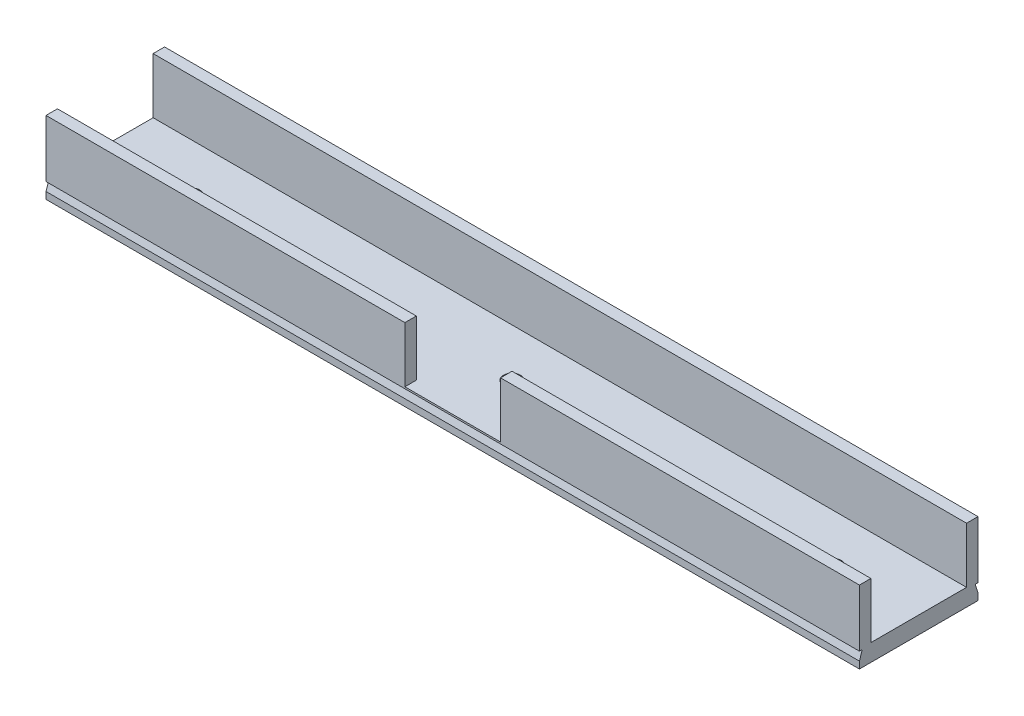
SolidWorks part; units mm, degrees
ref_plane "Front Plane" through (0, 0, 0) normal (0, 0, 1) x (1, 0, 0)
ref_plane "Top Plane" through (0, 0, 0) normal (0, 1, 0) x (1, 0, 0)
ref_plane "Right Plane" through (0, 0, 0) normal (1, 0, 0) x (0, 0, -1)
sketch "Croquis1" plane through (0, 0, 0) normal (0, 1, 0) x (1, 0, 0)
  line L0 (-71, -12.5) -> (-71, 12.5)
  line L1 (-71, -12.5) -> (71, -12.5)
  line L2 (-71, 12.5) -> (71, 12.5)
  line L3 (71, -12.5) -> (71, 12.5)
  line L4 (-71, -12.5) -> (71, 12.5) construction
  line L5 (-71, 12.5) -> (71, -12.5) construction
  line L6 (71, -10.35) -> (71, 10.35)
  line L7 (71, -10.35) -> (-71, -10.35)
  line L8 (71, 10.35) -> (-71, 10.35)
  line L9 (-71, -10.35) -> (-71, 10.35)
  line L10 (71, -10.35) -> (-71, 10.35) construction
  line L11 (71, 10.35) -> (-71, -10.35) construction
  point P1 (0, 0)
  point P2 (0, 0)
  dimension "D1" = 142
  dimension "D2" = 25
  dimension "D3" = 142
  dimension "D4" = 2.15
extrude "Saliente-Extruir2" add sketch "Croquis1" along normal blind 3 contours L3 L8 L0 L7
sketch "Croquis6" plane through (0, 3, 0) normal (0, 1, 0) x (1, 0, 0)
  line L0 (0, 0) -> (0, 6.8298) construction
  line L1 (-71, -10.35) -> (-71, 10.35) construction
  circle A0 centre (-56, 0) radius 1.5
  circle A1 centre (0, 0) radius 1.5
  circle A2 centre (56, 0) radius 1.5
  point P9 (-71, 0)
  dimension "D1" = 3
  dimension "D2" = 3
  dimension "D3" = 15
extrude "Cortar-Extruir4" cut sketch "Croquis6" against normal blind 3
sketch "Croquis7" plane through (0, 3, 0) normal (0, 1, 0) x (1, 0, 0)
  line L0 (-71, 8.35) -> (-71, 10.35)
  line L1 (-71, -10.35) -> (-71, 10.35) construction
  line L2 (-71, 10.35) -> (71, 10.35)
  line L3 (71, -10.35) -> (71, 10.35) construction
  line L4 (71, 10.35) -> (-71, 10.35) construction
  line L5 (71, 10.35) -> (71, 8.35)
  line L6 (71, 8.35) -> (-71, 8.35)
  line L7 (0, 0) -> (-103.6833, 0) construction
  line L8 (71, -8.35) -> (-71, -8.35)
  line L9 (71, -10.35) -> (71, -8.35)
  line L10 (-71, -10.35) -> (71, -10.35)
  line L11 (-71, -8.35) -> (-71, -10.35)
  dimension "D1" = 2
extrude "Saliente-Extruir3" add sketch "Croquis7" along normal blind 9.7
sketch "Croquis9" plane through (-71, 0, 0) normal (-1, 0, 0) x (0, 0, 1)
  line L1 (-10.35, 2.7) -> (-9.85, 2.7)
  line L2 (-10.35, 12.7) -> (-10.35, 0) construction
  line L3 (-9.85, 2.7) -> (-10.35, 1.2)
  line L4 (-10.35, 1.2) -> (-10.35, 2.7)
  line L5 (-10.35, 12.7) -> (-8.35, 12.7) construction
  line L6 (0, 0) -> (0, 4.8094) construction
  line L7 (10.35, 0) -> (-10.35, 0) construction
  line L8 (10.35, 2.7) -> (9.85, 2.7)
  line L9 (10.35, 1.2) -> (10.35, 2.7)
  line L10 (9.85, 2.7) -> (10.35, 1.2)
  dimension "D1" = 10
  dimension "D2" = 1.5
  dimension "D3" = 0.5
extrude "Cortar-Extruir5" cut sketch "Croquis9" against normal blind 224
sketch "Croquis10" plane through (0, 0, 10.35) normal (0, 0, 1) x (1, 0, 0)
  line L0 (-8.35, 3) -> (8.35, 3)
  line L1 (-8.35, 3) -> (-8.35, 12.7)
  line L2 (8.35, 3) -> (8.35, 12.7)
  line L3 (-8.35, 12.7) -> (8.35, 12.7)
  line L4 (-8.35, 3) -> (8.35, 12.7) construction
  line L5 (8.35, 3) -> (-8.35, 12.7) construction
  line L6 (71, 0) -> (-71, 0) construction
  point P1 (0, 7.85)
  point P3 (0, 0)
  point P8 (0, 0)
  dimension "D1" = 3
  dimension "D2" = 9.7
  dimension "D3" = 16.7
extrude "Cortar-Extruir6" cut sketch "Croquis10" against normal blind 10
